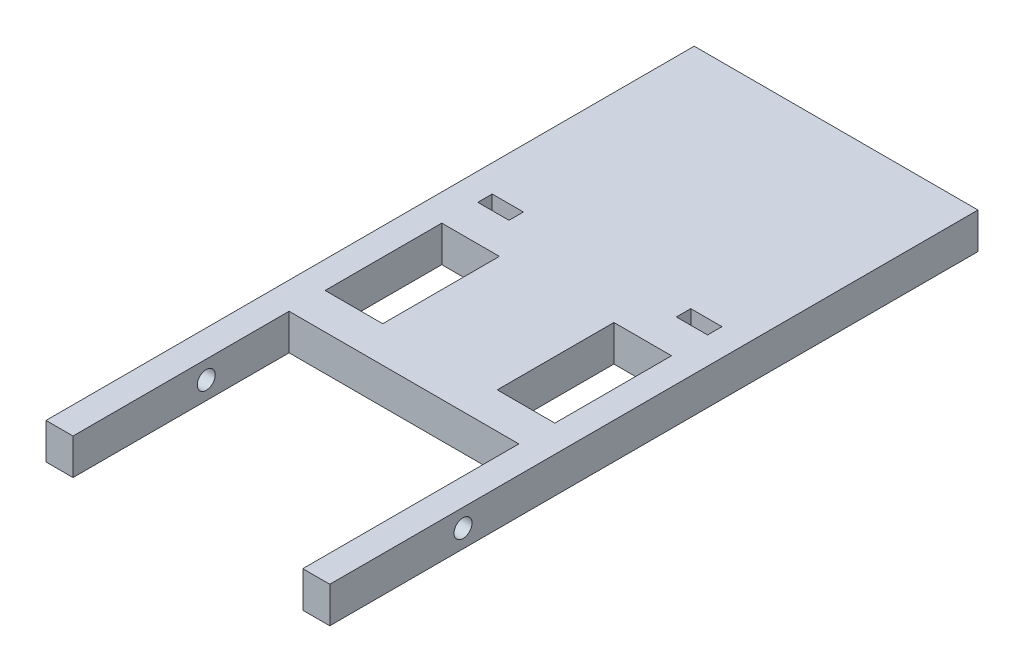
SolidWorks part; units mm, degrees
ref_plane "Front Plane" through (0, 0, 0) normal (0, 0, 1) x (1, 0, 0)
ref_plane "Top Plane" through (0, 0, 0) normal (0, 1, 0) x (1, 0, 0)
ref_plane "Right Plane" through (0, 0, 0) normal (1, 0, 0) x (0, 0, -1)
sketch "Sketch1" plane through (0, 0, 0) normal (0, 1, 0) x (1, 0, 0)
  line L1 (-50.038, 114.3) -> (50.038, 114.3)
  line L2 (-50.038, 114.3) -> (-50.038, -114.3)
  line L3 (-50.038, -114.3) -> (50.038, -114.3)
  line L4 (50.038, 114.3) -> (50.038, -114.3)
  line L5 (-50.038, 114.3) -> (50.038, -114.3) construction
  line L6 (-50.038, -114.3) -> (50.038, 114.3) construction
  point P0 (0, 0)
  dimension "D1" = 100.076
  dimension "D2" = 228.6
extrude "Boss-Extrude1" add sketch "Sketch1" along normal blind 12.7
sketch "Sketch2" plane through (0, 12.7, 0) normal (0, 1, 0) x (1, 0, 0)
  line L0 (-50.038, -114.3) -> (50.038, -114.3) construction
  line L1 (-40.513, -38.1) -> (40.513, -38.1)
  line L2 (-40.513, -38.1) -> (-40.513, -114.3)
  line L3 (-40.513, -114.3) -> (40.513, -114.3)
  line L4 (40.513, -38.1) -> (40.513, -114.3)
  line L5 (-50.038, 114.3) -> (-50.038, -114.3) construction
  line L6 (50.038, -114.3) -> (50.038, 114.3) construction
  dimension "D1" = 9.525
  dimension "D2" = 9.525
  dimension "D3" = 76.2
extrude "Cut-Extrude1" cut sketch "Sketch2" against normal through all
sketch "Sketch3" plane through (0, 12.7, 0) normal (0, 1, 0) x (1, 0, 0)
  line L0 (40.513, -38.1) -> (-40.513, -38.1) construction
  line L1 (-40.513, 15.748) -> (-20.193, 15.748)
  line L2 (-40.513, 15.748) -> (-40.513, -25.4)
  line L3 (-40.513, -25.4) -> (-20.193, -25.4)
  line L4 (-20.193, 15.748) -> (-20.193, -25.4)
  line L5 (-50.038, 114.3) -> (-50.038, -114.3) construction
  line L6 (0, 44.3201) -> (0, -22.352) construction
  line L7 (-40.513, 33.528) -> (-29.5148, 33.528)
  line L8 (-40.513, 33.528) -> (-40.513, 28.448)
  line L9 (-40.513, 28.448) -> (-29.5148, 28.448)
  line L10 (-29.5148, 33.528) -> (-29.5148, 28.448)
  line L11 (20.193, 15.748) -> (20.193, -25.4)
  line L12 (40.513, -25.4) -> (20.193, -25.4)
  line L13 (40.513, 15.748) -> (40.513, -25.4)
  line L14 (40.513, 15.748) -> (20.193, 15.748)
  line L15 (29.5148, 33.528) -> (29.5148, 28.448)
  line L16 (40.513, 28.448) -> (29.5148, 28.448)
  line L17 (40.513, 33.528) -> (40.513, 28.448)
  line L18 (40.513, 33.528) -> (29.5148, 33.528)
  dimension "D1" = 20.32
  dimension "D2" = 41.148
  dimension "D3" = 12.7
  dimension "D4" = 9.525
  dimension "D5" = 10.9982
  dimension "D6" = 5.08
  dimension "D7" = 9.525
  dimension "D8" = 12.7
extrude "Cut-Extrude2" cut sketch "Sketch3" against normal through all
sketch "Sketch4" plane through (-40.513, 0, 0) normal (1, 0, 0) x (0, 0, -1)
  line L0 (-38.1, 0) -> (-38.1, 12.7) construction
  line L1 (-38.1, 12.7) -> (-114.3, 12.7) construction
  circle A0 centre (-67.31, 6.35) radius 3.175
  dimension "D1" = 29.21
  dimension "D2" = 6.35
  dimension "D3" = 6.35
extrude "Cut-Extrude3" cut sketch "Sketch4" against normal through all both and the other way through all
